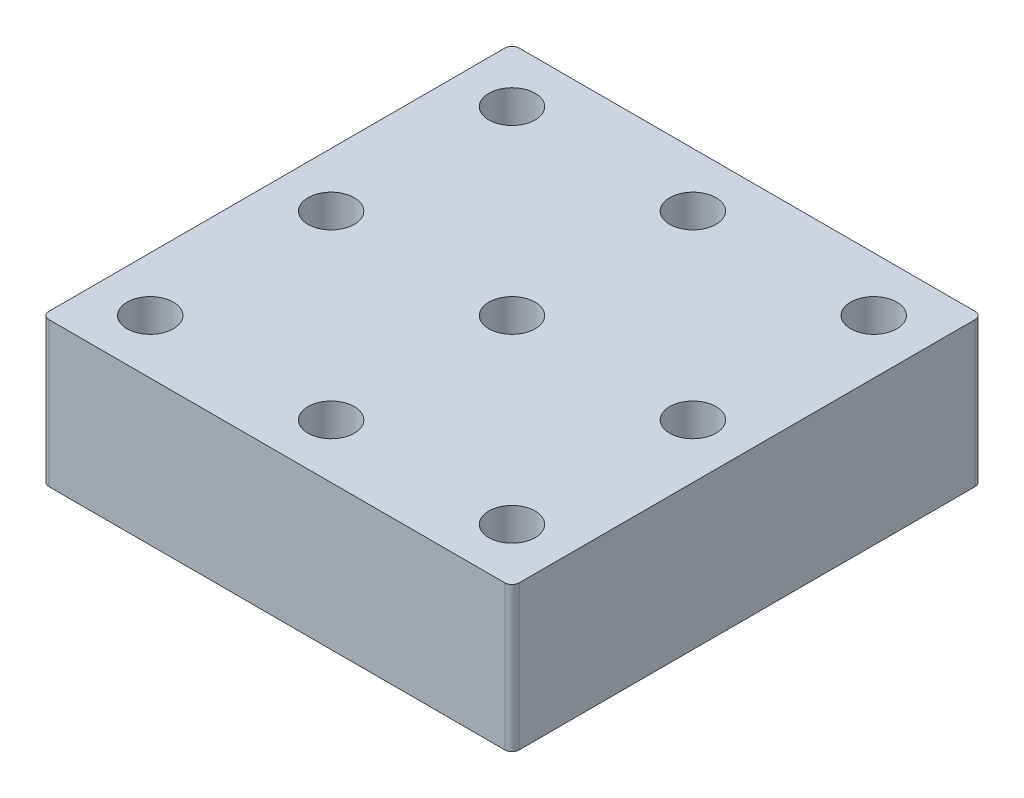
SolidWorks part; units mm, degrees
ref_plane "정면" through (0, 0, 0) normal (0, 0, 1) x (1, 0, 0)
ref_plane "윗면" through (0, 0, 0) normal (0, 1, 0) x (1, 0, 0)
ref_plane "우측면" through (0, 0, 0) normal (1, 0, 0) x (0, 0, -1)
sketch "스케치1" plane through (0, 0, 0) normal (0, 1, 0) x (1, 0, 0)
  line L1 (-32.5, 32.5) -> (32.5, 32.5)
  line L2 (-32.5, 32.5) -> (-32.5, -32.5)
  line L3 (-32.5, -32.5) -> (32.5, -32.5)
  line L4 (32.5, 32.5) -> (32.5, -32.5)
  point P4 (0, 32.5)
  point P6 (32.5, 0)
  dimension "D1" = 65
  dimension "D2" = 65
extrude "보스-돌출1" add sketch "스케치1" along normal blind 20
sketch "스케치2" plane through (0, 0, 0) normal (0, -1, 0) x (1, 0, 0)
  circle A0 centre (-25, 25) radius 3
  circle A1 centre (25, 25) radius 3
  circle A2 centre (25, -25) radius 3
  circle A3 centre (-25, -25) radius 3
  dimension "D5" = 6
  dimension "D1" = 50
  dimension "D2" = 50
  dimension "D3" = 25
  dimension "D4" = 25
extrude "컷-돌출1" cut sketch "스케치2" against normal blind 7.5
sketch "스케치3" plane through (0, 20, 0) normal (0, 1, 0) x (1, 0, 0)
  circle A0 centre (-25, 25) radius 3.2
  circle A1 centre (0, 25) radius 3.2
  circle A2 centre (25, 25) radius 3.2
  circle A3 centre (25, 0) radius 3.2
  circle A4 centre (25, -25) radius 3.2
  circle A5 centre (0, -25) radius 3.2
  circle A6 centre (-25, -25) radius 3.2
  circle A7 centre (-25, 0) radius 3.2
  circle A8 centre (0, 0) radius 3.2
  dimension "D1" = 6.4
  dimension "D2" = 25
  dimension "D3" = 25
  dimension "D4" = 25
  dimension "D5" = 25
extrude "컷-돌출2" cut sketch "스케치3" against normal blind 7.5
fillet "필렛1" radius 1 4 edges at (-32.5, 10, -32.5) (32.5, 10, -32.5) (32.5, 10, 32.5) (-32.5, 10, 32.5)
